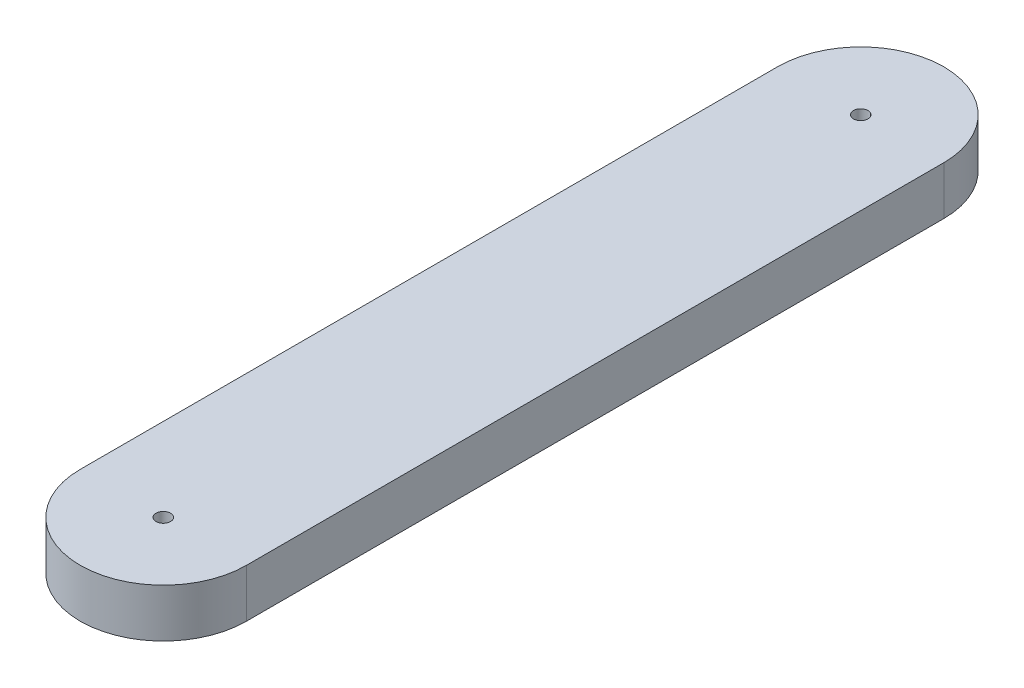
SolidWorks part; units mm, degrees
material "ABS PC"
ref_plane "Front Plane" through (0, 0, 0) normal (0, 0, 1) x (1, 0, 0)
ref_plane "Top Plane" through (0, 0, 0) normal (0, 1, 0) x (1, 0, 0)
ref_plane "Right Plane" through (0, 0, 0) normal (1, 0, 0) x (0, 0, -1)
sketch "Sketch2" plane through (0, 0, 0) normal (0, 1, 0) x (1, 0, 0)
  line L0 (0, 0) -> (-72, 0) construction
  line L3 (-36, 36) -> (-36, -36) construction
  line L4 (-27.42, 36) -> (-27.42, 8.582)
  line L5 (-44.58, 36) -> (-44.58, 8.582)
  line L8 (-27.42, -8.582) -> (-27.42, -36)
  line L9 (-44.58, -8.582) -> (-44.58, -36)
  line L10 (-27.42, -8.582) -> (-27.42, 8.582)
  line L11 (-44.58, -8.582) -> (-44.58, 8.582)
  arc A2 (-27.42, 36) -> (-44.58, 36) centre (-36, 36) ccw
  arc A3 (-44.58, -36) -> (-27.42, -36) centre (-36, -36) ccw
  point P3 (-36, 0)
  point P10 (-36, 0)
  dimension "D3" = 17.16
  dimension "D4" = 72
extrude "Boss-Extrude1" add sketch "Sketch2" along normal blind 5
sketch "Sketch3" plane through (0, 0, 0) normal (0, -1, 0) x (1, 0, 0)
  circle A0 centre (-36, 0) radius 0.75
  dimension "D1" = 1.5
extrude "Cut-Extrude1" cut sketch "Sketch3" against normal blind 3
sketch "Sketch4" plane through (0, 5, 0) normal (0, 1, 0) x (1, 0, 0)
  line L0 (-2.75, 0) -> (2.75, 0) construction
  circle A0 centre (-36, 36) radius 0.75
  circle A1 centre (-36, -36) radius 0.75
  dimension "D1" = 1.5
extrude "Cut-Extrude2" cut sketch "Sketch4" against normal blind 3
